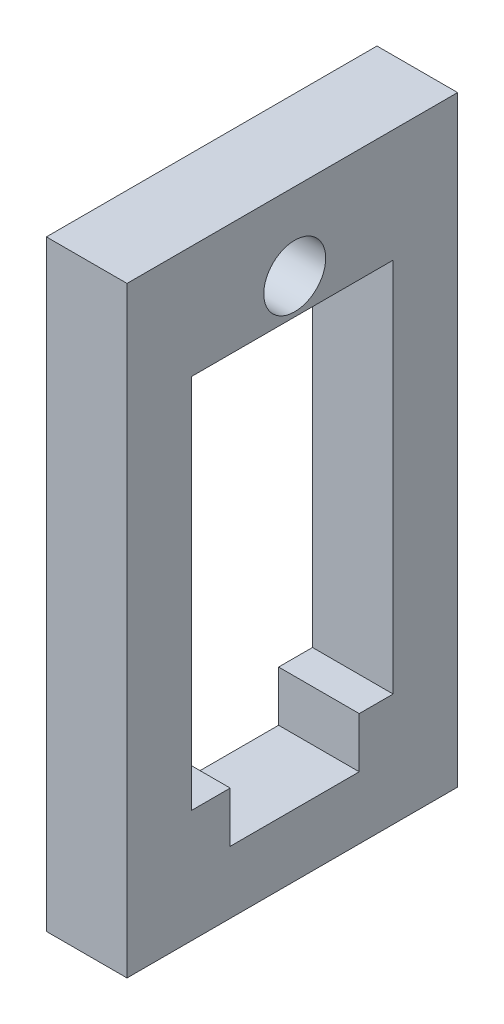
SolidWorks part; units mm, degrees
ref_plane "Front Plane" through (0, 0, 0) normal (0, 0, 1) x (1, 0, 0)
ref_plane "Top Plane" through (0, 0, 0) normal (0, 1, 0) x (1, 0, 0)
ref_plane "Right Plane" through (0, 0, 0) normal (1, 0, 0) x (0, 0, -1)
sketch "Sketch1" plane through (0, 0, 0) normal (1, 0, 0) x (0, 0, -1)
  line L1 (-10.4, -19.05) -> (10.1, -19.05)
  line L2 (-10.4, -19.05) -> (-10.4, 18.25)
  line L3 (-10.4, 18.25) -> (10.1, 18.25)
  line L4 (10.1, -19.05) -> (10.1, 18.25)
  line L7 (-6.4, -12.05) -> (6.1, -12.05)
  line L8 (-6.4, -12.05) -> (-6.4, 11.25)
  line L9 (-6.4, 11.25) -> (6.1, 11.25)
  line L10 (6.1, -12.05) -> (6.1, 11.25)
  line L11 (-6.4, -12.05) -> (6.1, 11.25) construction
  line L12 (-6.4, 11.25) -> (6.1, -12.05) construction
  point P0 (0, 0)
  point P6 (-0.15, -0.4)
  dimension "D1" = 12.5
  dimension "D2" = 23.3
  dimension "D3" = 4
  dimension "D4" = 7
  dimension "D5" = 7
  dimension "D6" = 4
extrude "Boss-Extrude1" add sketch "Sketch1" along normal blind 5
sketch "Sketch2" plane through (5, 0, 0) normal (1, 0, 0) x (0, 0, -1)
  line L0 (6.1, 11.25) -> (-6.4, 11.25) construction
  circle A0 centre (0, 13.45) radius 1.92
  dimension "D1" = 3.84
  dimension "D2" = 2.2
extrude "Cut-Extrude1" cut sketch "Sketch2" against normal blind 13
sketch "Sketch4" plane through (5, 0, 0) normal (1, 0, 0) x (0, 0, -1)
  line L0 (0, -7.6507) -> (0, -19.6626) construction
  line L1 (4, -12.05) -> (-4, -12.05)
  line L2 (-6.4, -12.05) -> (6.1, -12.05) construction
  line L3 (-4, -12.05) -> (-4, -15.1768)
  line L5 (-4, -15.1768) -> (4, -15.1768)
  line L6 (4, -12.05) -> (4, -15.1768)
  point P12 (0, -15.1768)
  point P13 (0, -12.05)
  dimension "D1" = 8
extrude "Cut-Extrude3" cut sketch "Sketch4" against normal blind 20
